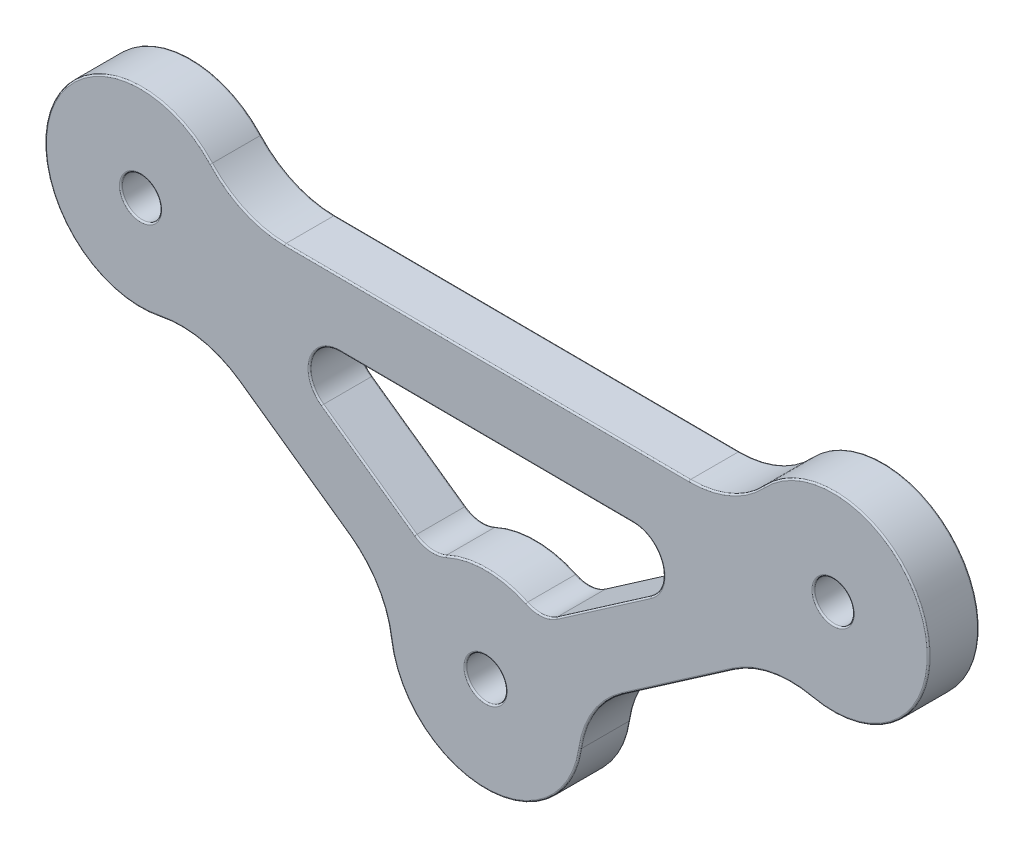
SolidWorks part; units mm, degrees
ref_plane "Front Plane" through (0, 0, 0) normal (0, 0, 1) x (1, 0, 0)
ref_plane "Top Plane" through (0, 0, 0) normal (0, 1, 0) x (1, 0, 0)
ref_plane "Right Plane" through (0, 0, 0) normal (1, 0, 0) x (0, 0, -1)
sketch "Sketch1" plane through (0, 0, 0) normal (0, 0, 1) x (1, 0, 0)
  line L0 (-2.5448, 302.8447) -> (-71.3526, 303.2131) construction
  line L1 (-2.5448, 302.8447) -> (-71.3526, 303.2131) construction
  line L2 (-71.3526, 303.2131) -> (-37.0777, 278.939) construction
  line L3 (-71.3526, 303.2131) -> (-37.0777, 278.939) construction
  line L4 (-37.0777, 278.939) -> (-2.5448, 302.8447) construction
  line L5 (-37.0777, 278.939) -> (-2.5448, 302.8447) construction
  circle A0 centre (-71.3526, 303.2131) radius 9.5
  circle A1 centre (-37.0777, 278.939) radius 9.5
  circle A2 centre (-2.5448, 302.8447) radius 9.5
  circle A3 centre (-71.3526, 303.2131) radius 1.95
  circle A4 centre (-2.5448, 302.8447) radius 1.95
  circle A5 centre (-37.0777, 278.939) radius 2
  dimension "D1" = 19
  dimension "D2" = 4
  dimension "D3" = 3.9
extrude "Boss-Extrude1" add sketch "Sketch1" against normal blind 5
sketch "Sketch2" plane through (0, 0, 0) normal (0, 0, 1) x (1, 0, 0)
  line L0 (-66.4562, 299.7454) -> (-41.9741, 282.4068)
  line L1 (-71.3526, 303.2131) -> (-37.0777, 278.939) construction
  line L2 (-64.4487, 303.1761) -> (-9.4487, 302.8817)
  line L3 (-2.5448, 302.8447) -> (-71.3526, 303.2131) construction
  line L4 (-7.4781, 299.4296) -> (-32.1444, 282.3541)
  line L5 (-37.0777, 278.939) -> (-2.5448, 302.8447) construction
  point P12 (-54.2151, 291.0761)
  point P13 (-19.8112, 290.8919)
  point P14 (-36.9487, 303.0289)
  dimension "D1" = 55
  dimension "D2" = 30
extrude "Extrude-Thin1" add sketch "Sketch2" against normal blind 5 thin thin type mid plane wall 6.5
fillet "Fillet1" radius 3 4 edges at (-61.0624, 299.908, -2.5) (-12.8697, 299.6499, -2.5) (-31.5878, 286.6922, -2.5) (-42.4842, 286.7505, -2.5)
fillet "Fillet2" radius 10 6 edges at (-46.2409, 281.4461, -2.5) (-65.946, 295.4016, -2.5) (-27.8881, 281.3478, -2.5) (-8.0346, 295.0915, -2.5) (-11.454, 306.1424, -2.5) (-62.4085, 306.4153, -2.5)
fillet "Fillet3" radius 0.15 46 edges at (-0.5948, 302.8447, -5) (-35.0777, 278.939, -5) (-69.4026, 303.2131, -5) (-12.8265, 306.9861, -5) (-36.9313, 306.2788, 0) (-36.9313, 306.2788, -5) (-61.0271, 307.2441, -5) (-80.3975, 306.1183, -5) (-65.3057, 293.9234, -5) (-56.0935, 288.4238, -5) (-56.0935, 288.4238, 0) (-47.8479, 281.5594, -5) (-37.1285, 269.4392, -5) (-26.28, 281.444, -5) (-17.9614, 288.2197, 0) (-17.9614, 288.2197, -5) (-8.6908, 293.6203, -5) (6.5307, 305.6529, -5) (-31.4889, 287.2495, -5) (-37.0268, 288.4389, -5) (-42.5771, 287.3089, -5) (-48.6656, 291.1283, -5) (-48.6656, 291.1283, 0) (-54.4201, 297.7745, -5) (-36.9661, 299.7789, 0) (-36.9661, 299.7789, -5) (-19.5345, 297.5877, -5) (-25.3598, 291.0035, 0) (-25.3598, 291.0035, -5) (-0.5948, 302.8447, 0) (-35.0777, 278.939, 0) (-69.4026, 303.2131, 0) (-26.28, 281.444, 0) (-37.1285, 269.4392, 0) (-47.8479, 281.5594, 0) (-65.3057, 293.9234, 0) (-80.3975, 306.1183, 0) (-61.0271, 307.2441, 0) (-12.8265, 306.9861, 0) (6.5307, 305.6529, 0) (-8.6908, 293.6203, 0) (-42.5771, 287.3089, 0) (-37.0268, 288.4389, 0) (-31.4889, 287.2495, 0) (-19.5345, 297.5877, 0) (-54.4201, 297.7745, 0)
